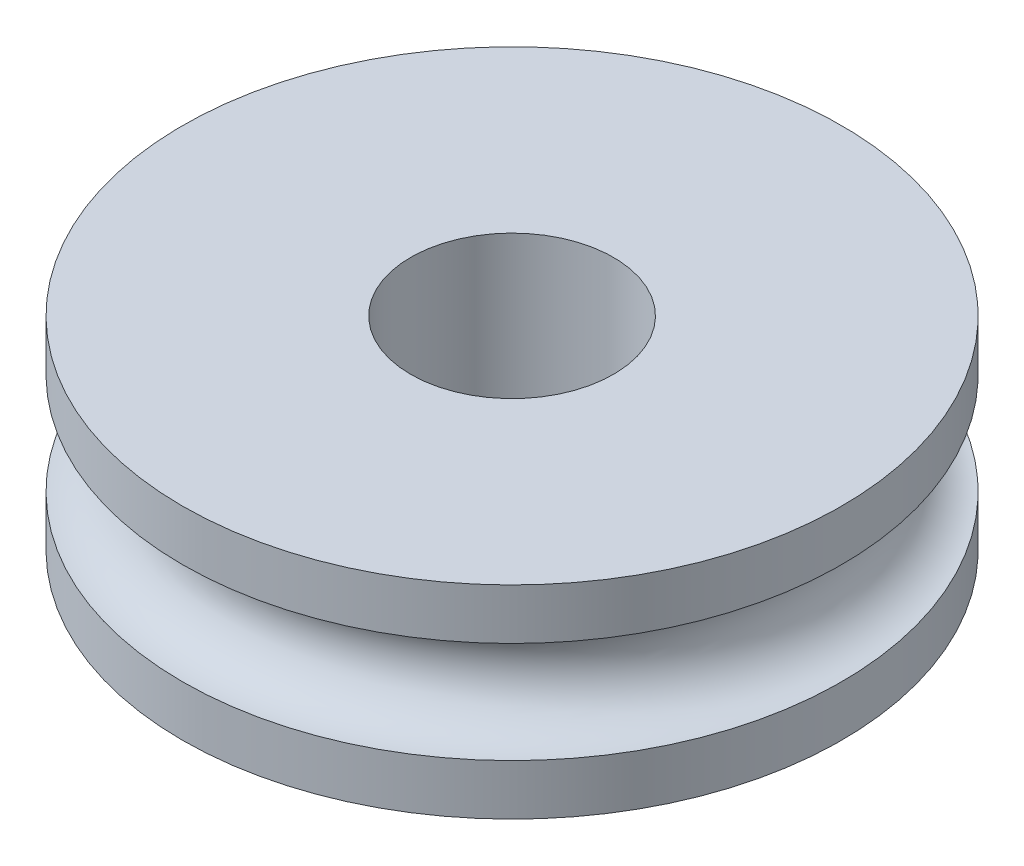
SolidWorks part; units mm, degrees
ref_plane "Front Plane" through (0, 0, 0) normal (0, 0, 1) x (1, 0, 0)
ref_plane "Top Plane" through (0, 0, 0) normal (0, 1, 0) x (1, 0, 0)
ref_plane "Right Plane" through (0, 0, 0) normal (1, 0, 0) x (0, 0, -1)
ref_plane "Plane1" through (0, 0, -44.43) normal (0, 0, -1) x (-1, 0, 0)
sketch "Sketch1" plane through (0, 0, -44.43) normal (0, 0, -1) x (-1, 0, 0)
  line L0 (-81, 54.5264) -> (-81, 53.5264)
  line L1 (-81, 51.5264) -> (-81, 50.5264)
  line L2 (-81, 50.5264) -> (-76.5, 50.5264)
  line L3 (-76.5, 50.5264) -> (-76.5, 54.5264)
  line L4 (-76.5, 54.5264) -> (-81, 54.5264)
  line L5 (-74.5, 50.5264) -> (-74.5, 54.5264) construction
  arc A0 (-81, 53.5264) -> (-81, 51.5264) centre (-81, 52.5264) cw
revolve "Revolve1" add sketch "Sketch1" angle 360 about L5
ref_plane "Plane2" through (0, 52.5264, 0) normal (0, 1, 0) x (1, 0, 0)
